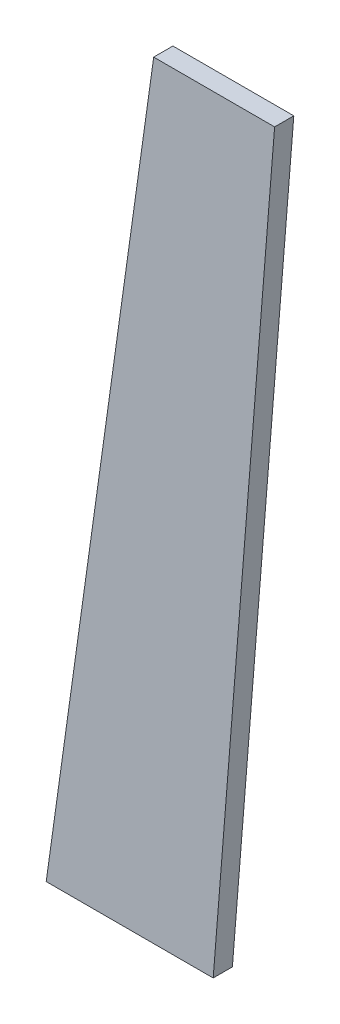
SolidWorks part; units mm, degrees
material "ABS"
ref_plane "Front Plane" through (0, 0, 0) normal (0, 0, 1) x (1, 0, 0)
ref_plane "Top Plane" through (0, 0, 0) normal (0, 1, 0) x (1, 0, 0)
ref_plane "Right Plane" through (0, 0, 0) normal (1, 0, 0) x (0, 0, -1)
sketch "Sketch1" plane through (0, 0, 0) normal (0, 0, 1) x (1, 0, 0)
  line L0 (0, 0) -> (63.517, 0) construction
  line L1 (63.517, 0) -> (83.517, 250) construction
  line L2 (83.517, 250) -> (-16.4828, 250) construction
  line L3 (-16.4828, 250) -> (0, 0) construction
  line L4 (63.517, 0) -> (18.517, 0) construction
  line L5 (83.517, 250) -> (53.517, 250) construction
  line L6 (53.517, 250) -> (18.517, 0) construction
  line L7 (53.517, 250) -> (53.517, 0) construction
  line L8 (53.517, 0) -> (53.517, 25) construction
  line L9 (53.517, 250) -> (53.517, 225) construction
  line L10 (65.517, 25) -> (22.017, 25)
  line L11 (22.017, 25) -> (50.017, 225)
  line L12 (50.017, 225) -> (81.517, 225)
  line L13 (81.517, 225) -> (65.517, 25)
  dimension "D1" = 45
  dimension "D2" = 25
  dimension "D3" = 25
extrude "Boss-Extrude1" add sketch "Sketch1" along normal blind 5
